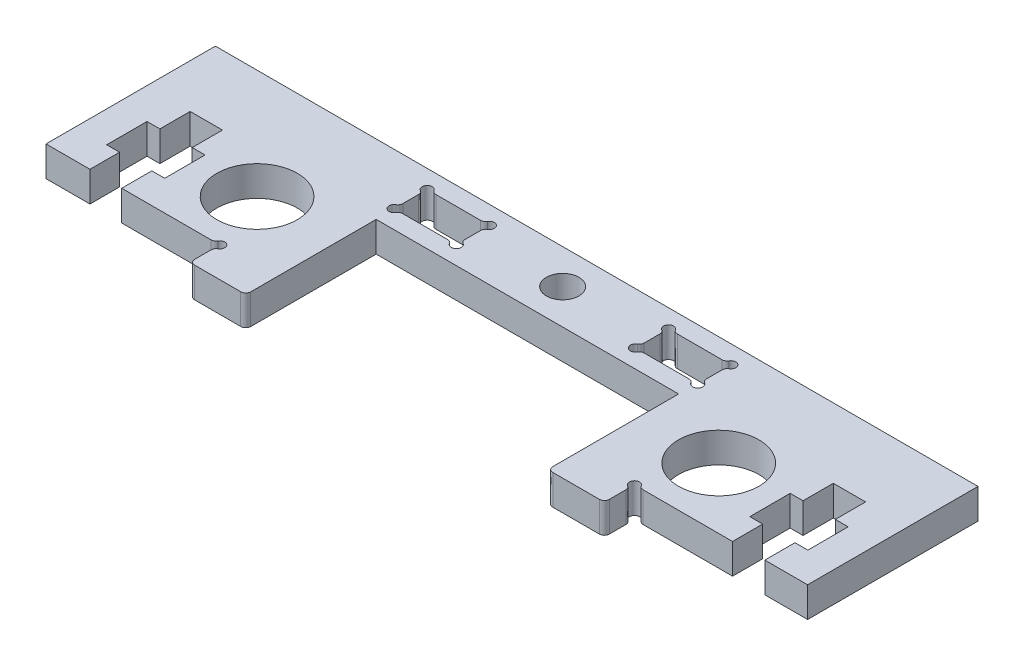
SolidWorks part; units mm, degrees
ref_plane "Front Plane" through (0, 0, 0) normal (0, 0, 1) x (1, 0, 0)
ref_plane "Top Plane" through (0, 0, 0) normal (0, 1, 0) x (1, 0, 0)
ref_plane "Right Plane" through (0, 0, 0) normal (1, 0, 0) x (0, 0, -1)
sketch "Sketch1" plane through (0, 0, 0) normal (0, 1, 0) x (1, 0, 0)
  line L0 (22.9871, 18.2293) -> (22.9871, 7.325)
  line L1 (22.9871, 18.2293) -> (22.9871, 7.325)
  line L2 (38.402, 11.1937) -> (38.402, 8.191)
  line L3 (38.402, 11.1937) -> (38.402, 8.191)
  line L4 (41.6191, 11.1937) -> (41.6191, 8.191)
  line L5 (41.6191, 11.1937) -> (41.6191, 8.191)
  line L6 (41.6191, 15.2151) -> (41.6191, 18.2311)
  line L7 (41.6191, 15.2151) -> (41.6191, 18.2311)
  line L8 (41.6191, 18.2311) -> (38.402, 18.2311)
  line L9 (41.6191, 18.2311) -> (38.402, 18.2311)
  line L10 (38.402, 18.2311) -> (38.402, 15.2151)
  line L11 (38.402, 18.2311) -> (38.402, 15.2151)
  line L12 (42.9009, 11.1937) -> (42.9009, 15.2151)
  line L13 (42.9009, 11.1937) -> (42.9009, 15.2151)
  line L14 (37.1202, 15.2151) -> (37.1202, 11.1937)
  line L15 (37.1202, 15.2151) -> (37.1202, 11.1937)
  line L16 (41.6191, 8.191) -> (45.8799, 8.191)
  line L17 (41.6191, 8.191) -> (45.8799, 8.191)
  line L18 (38.402, 15.2151) -> (37.1202, 15.2151)
  line L19 (38.402, 15.2151) -> (37.1202, 15.2151)
  line L20 (42.9009, 15.2151) -> (41.6191, 15.2151)
  line L21 (42.9009, 15.2151) -> (41.6191, 15.2151)
  line L22 (41.6191, 11.1937) -> (42.9009, 11.1937)
  line L23 (41.6191, 11.1937) -> (42.9009, 11.1937)
  line L24 (37.1202, 11.1937) -> (38.402, 11.1937)
  line L25 (37.1202, 11.1937) -> (38.402, 11.1937)
  line L26 (22.2079, 23.3482) -> (17.7399, 23.3482)
  line L27 (22.2079, 23.3482) -> (17.7399, 23.3482)
  line L28 (17.7399, 20.0482) -> (22.2079, 20.0482)
  line L29 (17.7399, 20.0482) -> (22.2079, 20.0482)
  line L30 (23.0739, 20.9143) -> (23.0739, 22.4821)
  line L31 (23.0739, 20.9143) -> (23.0739, 22.4821)
  line L32 (16.8739, 22.4821) -> (16.8739, 20.9143)
  line L33 (16.8739, 22.4821) -> (16.8739, 20.9143)
  line L34 (28.1294, 5.191) -> (23.4871, 5.191)
  line L35 (28.1294, 5.191) -> (23.4871, 5.191)
  line L36 (28.6294, 7.325) -> (28.6294, 5.691)
  line L37 (28.6294, 7.325) -> (28.6294, 5.691)
  line L38 (22.9871, 7.325) -> (22.9871, 5.691)
  line L39 (22.9871, 7.325) -> (22.9871, 5.691)
  line L40 (29.4954, 8.191) -> (38.402, 8.191)
  line L41 (29.4954, 8.191) -> (38.402, 8.191)
  line L42 (45.8799, 25.1711) -> (45.8799, 8.191)
  line L43 (45.8799, 25.1711) -> (45.8799, 8.191)
  line L44 (-29.9892, 25.1711) -> (45.8799, 25.1711)
  line L45 (-29.9892, 25.1711) -> (45.8799, 25.1711)
  line L46 (-7.1439, 18.2293) -> (-7.1439, 7.325)
  line L47 (-7.1439, 18.2293) -> (-7.1439, 7.325)
  line L48 (-22.5116, 11.2388) -> (-22.5116, 8.236)
  line L49 (-22.5116, 11.2388) -> (-22.5116, 8.236)
  line L50 (-25.7287, 11.2388) -> (-25.7287, 8.236)
  line L51 (-25.7287, 11.2388) -> (-25.7287, 8.236)
  line L52 (-25.7287, 15.2601) -> (-25.7287, 18.2762)
  line L53 (-25.7287, 15.2601) -> (-25.7287, 18.2762)
  line L54 (-25.7287, 18.2762) -> (-22.5116, 18.2762)
  line L55 (-25.7287, 18.2762) -> (-22.5116, 18.2762)
  line L56 (-22.5116, 18.2762) -> (-22.5116, 15.2601)
  line L57 (-22.5116, 18.2762) -> (-22.5116, 15.2601)
  line L58 (-27.0105, 11.2388) -> (-27.0105, 15.2601)
  line L59 (-27.0105, 11.2388) -> (-27.0105, 15.2601)
  line L60 (-21.2298, 15.2601) -> (-21.2298, 11.2388)
  line L61 (-21.2298, 15.2601) -> (-21.2298, 11.2388)
  line L62 (-25.6909, 8.292) -> (-30.109, 8.292)
  line L63 (-25.6909, 8.292) -> (-30.109, 8.292)
  line L64 (-22.5116, 15.2601) -> (-21.2298, 15.2601)
  line L65 (-22.5116, 15.2601) -> (-21.2298, 15.2601)
  line L66 (-27.0105, 15.2601) -> (-25.7287, 15.2601)
  line L67 (-27.0105, 15.2601) -> (-25.7287, 15.2601)
  line L68 (-25.7287, 11.2388) -> (-27.0105, 11.2388)
  line L69 (-25.7287, 11.2388) -> (-27.0105, 11.2388)
  line L70 (-21.2298, 11.2388) -> (-22.5116, 11.2388)
  line L71 (-21.2298, 11.2388) -> (-22.5116, 11.2388)
  line L72 (-6.3172, 23.3482) -> (-1.8492, 23.3482)
  line L73 (-6.3172, 23.3482) -> (-1.8492, 23.3482)
  line L74 (-1.8492, 20.0482) -> (-6.3172, 20.0482)
  line L75 (-1.8492, 20.0482) -> (-6.3172, 20.0482)
  line L76 (-7.1832, 20.9143) -> (-7.1832, 22.4821)
  line L77 (-7.1832, 20.9143) -> (-7.1832, 22.4821)
  line L78 (-0.9832, 22.4821) -> (-0.9832, 20.9143)
  line L79 (-0.9832, 22.4821) -> (-0.9832, 20.9143)
  line L80 (-12.2415, 5.236) -> (-7.6539, 5.236)
  line L81 (-12.2415, 5.236) -> (-7.6539, 5.236)
  line L82 (-12.7415, 7.37) -> (-12.7415, 5.736)
  line L83 (-12.7415, 7.37) -> (-12.7415, 5.736)
  line L84 (-7.1439, 7.325) -> (-7.1439, 5.691)
  line L85 (-7.1439, 7.325) -> (-7.1439, 5.691)
  line L86 (-13.605, 8.236) -> (-22.5116, 8.236)
  line L87 (-13.605, 8.236) -> (-22.5116, 8.236)
  line L88 (-30.109, 25.0536) -> (-30.109, 8.292)
  line L89 (-30.109, 25.0536) -> (-30.109, 8.292)
  line L90 (-7.1439, 18.2293) -> (22.9871, 18.2293)
  line L91 (-7.1439, 18.2293) -> (22.9871, 18.2293)
  arc A0 (16.6239, 20.4813) -> (17.3069, 19.7982) centre (16.8739, 20.0482) ccw
  arc A1 (16.6239, 20.4813) -> (17.3069, 19.7982) centre (16.8739, 20.0482) ccw
  circle A2 centre (30.9463, 14.2702) radius 4.0093
  circle A3 centre (30.9463, 14.2702) radius 4.0093
  arc A4 (23.3239, 22.9151) -> (23.0739, 22.4821) centre (23.5739, 22.4821) ccw
  arc A5 (23.3239, 22.9151) -> (23.0739, 22.4821) centre (23.5739, 22.4821) ccw
  arc A6 (23.3239, 22.9151) -> (22.6409, 23.5982) centre (23.0739, 23.3482) ccw
  arc A7 (23.3239, 22.9151) -> (22.6409, 23.5982) centre (23.0739, 23.3482) ccw
  arc A8 (22.2079, 23.3482) -> (22.6409, 23.5982) centre (22.2079, 23.8482) ccw
  arc A9 (22.2079, 23.3482) -> (22.6409, 23.5982) centre (22.2079, 23.8482) ccw
  arc A10 (17.7399, 20.0482) -> (17.3069, 19.7982) centre (17.7399, 19.5482) ccw
  arc A11 (17.7399, 20.0482) -> (17.3069, 19.7982) centre (17.7399, 19.5482) ccw
  arc A12 (17.3069, 23.5982) -> (16.6239, 22.9151) centre (16.8739, 23.3482) ccw
  arc A13 (17.3069, 23.5982) -> (16.6239, 22.9151) centre (16.8739, 23.3482) ccw
  arc A14 (16.6239, 20.4813) -> (16.8739, 20.9143) centre (16.3739, 20.9143) ccw
  arc A15 (16.6239, 20.4813) -> (16.8739, 20.9143) centre (16.3739, 20.9143) ccw
  arc A16 (23.0739, 20.9143) -> (23.3239, 20.4813) centre (23.5739, 20.9143) ccw
  arc A17 (23.0739, 20.9143) -> (23.3239, 20.4813) centre (23.5739, 20.9143) ccw
  arc A18 (17.3069, 23.5982) -> (17.7399, 23.3482) centre (17.7399, 23.8482) ccw
  arc A19 (17.3069, 23.5982) -> (17.7399, 23.3482) centre (17.7399, 23.8482) ccw
  arc A20 (22.6409, 19.7982) -> (22.2079, 20.0482) centre (22.2079, 19.5482) ccw
  arc A21 (22.6409, 19.7982) -> (22.2079, 20.0482) centre (22.2079, 19.5482) ccw
  arc A22 (16.8739, 22.4821) -> (16.6239, 22.9151) centre (16.3739, 22.4821) ccw
  arc A23 (16.8739, 22.4821) -> (16.6239, 22.9151) centre (16.3739, 22.4821) ccw
  arc A24 (22.6409, 19.7982) -> (23.3239, 20.4813) centre (23.0739, 20.0482) ccw
  arc A25 (22.6409, 19.7982) -> (23.3239, 20.4813) centre (23.0739, 20.0482) ccw
  arc A26 (29.0624, 8.441) -> (29.4954, 8.191) centre (29.4954, 8.691) ccw
  arc A27 (29.0624, 8.441) -> (29.4954, 8.191) centre (29.4954, 8.691) ccw
  arc A28 (29.0624, 8.441) -> (28.3794, 7.758) centre (28.6294, 8.191) ccw
  arc A29 (29.0624, 8.441) -> (28.3794, 7.758) centre (28.6294, 8.191) ccw
  arc A30 (28.6294, 7.325) -> (28.3794, 7.758) centre (28.1294, 7.325) ccw
  arc A31 (28.6294, 7.325) -> (28.3794, 7.758) centre (28.1294, 7.325) ccw
  arc A32 (28.1294, 5.191) -> (28.6294, 5.691) centre (28.1294, 5.691) ccw
  arc A33 (28.1294, 5.191) -> (28.6294, 5.691) centre (28.1294, 5.691) ccw
  arc A34 (22.9871, 5.691) -> (23.4871, 5.191) centre (23.4871, 5.691) ccw
  arc A35 (22.9871, 5.691) -> (23.4871, 5.191) centre (23.4871, 5.691) ccw
  arc A36 (-13.605, 8.236) -> (-13.1745, 8.486) centre (-13.6076, 8.736) ccw
  arc A37 (-13.605, 8.236) -> (-13.1745, 8.486) centre (-13.6076, 8.736) ccw
  arc A38 (-12.4915, 7.803) -> (-13.1745, 8.486) centre (-12.7415, 8.236) ccw
  arc A39 (-12.4915, 7.803) -> (-13.1745, 8.486) centre (-12.7415, 8.236) ccw
  arc A40 (-12.4915, 7.803) -> (-12.7415, 7.37) centre (-12.2415, 7.37) ccw
  arc A41 (-12.4915, 7.803) -> (-12.7415, 7.37) centre (-12.2415, 7.37) ccw
  arc A42 (-1.4162, 19.7982) -> (-0.7332, 20.4813) centre (-0.9832, 20.0482) ccw
  arc A43 (-1.4162, 19.7982) -> (-0.7332, 20.4813) centre (-0.9832, 20.0482) ccw
  circle A44 centre (-15.0556, 14.2702) radius 4.0093
  circle A45 centre (-15.0556, 14.2702) radius 4.0093
  circle A46 centre (7.9453, 21.7153) radius 1.6197
  circle A47 centre (7.9453, 21.7153) radius 1.6197
  arc A48 (-7.1832, 22.4821) -> (-7.4332, 22.9151) centre (-7.6832, 22.4821) ccw
  arc A49 (-7.1832, 22.4821) -> (-7.4332, 22.9151) centre (-7.6832, 22.4821) ccw
  arc A50 (-6.7502, 23.5982) -> (-7.4332, 22.9151) centre (-7.1832, 23.3482) ccw
  arc A51 (-6.7502, 23.5982) -> (-7.4332, 22.9151) centre (-7.1832, 23.3482) ccw
  arc A52 (-6.7502, 23.5982) -> (-6.3172, 23.3482) centre (-6.3172, 23.8482) ccw
  arc A53 (-6.7502, 23.5982) -> (-6.3172, 23.3482) centre (-6.3172, 23.8482) ccw
  arc A54 (-1.4162, 19.7982) -> (-1.8492, 20.0482) centre (-1.8492, 19.5482) ccw
  arc A55 (-1.4162, 19.7982) -> (-1.8492, 20.0482) centre (-1.8492, 19.5482) ccw
  arc A56 (-0.7332, 22.9151) -> (-1.4162, 23.5982) centre (-0.9832, 23.3482) ccw
  arc A57 (-0.7332, 22.9151) -> (-1.4162, 23.5982) centre (-0.9832, 23.3482) ccw
  arc A58 (-0.9832, 20.9143) -> (-0.7332, 20.4813) centre (-0.4832, 20.9143) ccw
  arc A59 (-0.9832, 20.9143) -> (-0.7332, 20.4813) centre (-0.4832, 20.9143) ccw
  arc A60 (-7.4332, 20.4813) -> (-7.1832, 20.9143) centre (-7.6832, 20.9143) ccw
  arc A61 (-7.4332, 20.4813) -> (-7.1832, 20.9143) centre (-7.6832, 20.9143) ccw
  arc A62 (-1.8492, 23.3482) -> (-1.4162, 23.5982) centre (-1.8492, 23.8482) ccw
  arc A63 (-1.8492, 23.3482) -> (-1.4162, 23.5982) centre (-1.8492, 23.8482) ccw
  arc A64 (-6.3172, 20.0482) -> (-6.7502, 19.7982) centre (-6.3172, 19.5482) ccw
  arc A65 (-6.3172, 20.0482) -> (-6.7502, 19.7982) centre (-6.3172, 19.5482) ccw
  arc A66 (-0.7332, 22.9151) -> (-0.9832, 22.4821) centre (-0.4832, 22.4821) ccw
  arc A67 (-0.7332, 22.9151) -> (-0.9832, 22.4821) centre (-0.4832, 22.4821) ccw
  arc A68 (-7.4332, 20.4813) -> (-6.7502, 19.7982) centre (-7.1832, 20.0482) ccw
  arc A69 (-7.4332, 20.4813) -> (-6.7502, 19.7982) centre (-7.1832, 20.0482) ccw
  arc A70 (-12.7415, 5.736) -> (-12.2415, 5.236) centre (-12.2415, 5.736) ccw
  arc A71 (-12.7415, 5.736) -> (-12.2415, 5.236) centre (-12.2415, 5.736) ccw
  arc A72 (-7.6539, 5.236) -> (-7.1439, 5.691) centre (-7.6418, 5.7358) ccw
  arc A73 (-7.6539, 5.236) -> (-7.1439, 5.691) centre (-7.6418, 5.7358) ccw
  arc A74 (-29.9892, 25.1711) -> (-30.109, 25.0536) centre (-30.0018, 25.0641) ccw
  arc A75 (-29.9892, 25.1711) -> (-30.109, 25.0536) centre (-30.0018, 25.0641) ccw
  point P108 (0, 0)
  point P110 (0, 0)
  point P129 (0, 0)
  point P130 (0, 0)
  point P131 (0, 0)
  point P132 (0, 0)
  point P133 (23.4901, 5.191)
  point P134 (0, 0)
  point P135 (0, 0)
  point P136 (0, 0)
  point P137 (0, 0)
  point P138 (0, 0)
  point P139 (0, 0)
  point P140 (0, 0)
  point P141 (0, 0)
  point P142 (0, 0)
  point P143 (0, 0)
  point P144 (41.5786, 8.2218)
  point P145 (0, 0)
  point P146 (0, 0)
  point P147 (0, 0)
  point P148 (-7.65, 5.236)
extrude "Boss-Extrude1" add sketch "Sketch1" along normal blind 3 contours L44 A74 L88 L62 L50 L68 L58 L66 L52 L54 L56 L64 L60 L70 L48 L86 A36 A38 A40 L82 A70 L80 A72 L84 L46 L90 L0 L38 A34 L34 A32 L36 A30 A28 A26 L40 L2 L24 L14 L18 L10 L8 L6 L20 L12 L22 L4 L16 L42 A2
